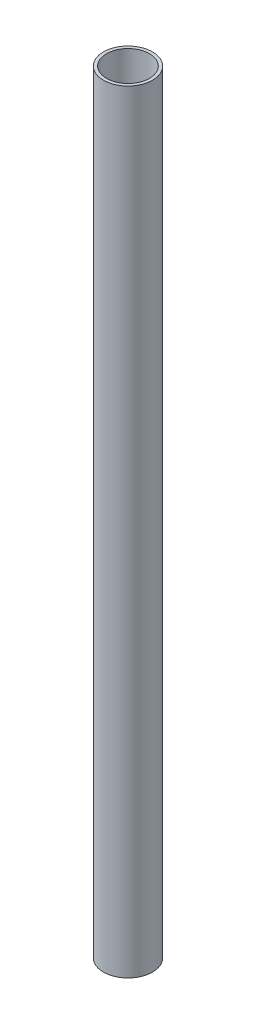
SolidWorks part; units mm, degrees
ref_plane "Front Plane" through (0, 0, 0) normal (0, 0, 1) x (1, 0, 0)
ref_plane "Top Plane" through (0, 0, 0) normal (0, 1, 0) x (1, 0, 0)
ref_plane "Right Plane" through (0, 0, 0) normal (1, 0, 0) x (0, 0, -1)
sketch "Sketch1" plane through (0, 0, 0) normal (0, 1, 0) x (1, 0, 0)
  circle A0 centre (0, 0) radius 12.7
  circle A1 centre (0, 0) radius 11.1125
  dimension "D1" = 25.4
  dimension "D2" = 22.225
extrude "Boss-Extrude1" add sketch "Sketch1" along normal blind 400
